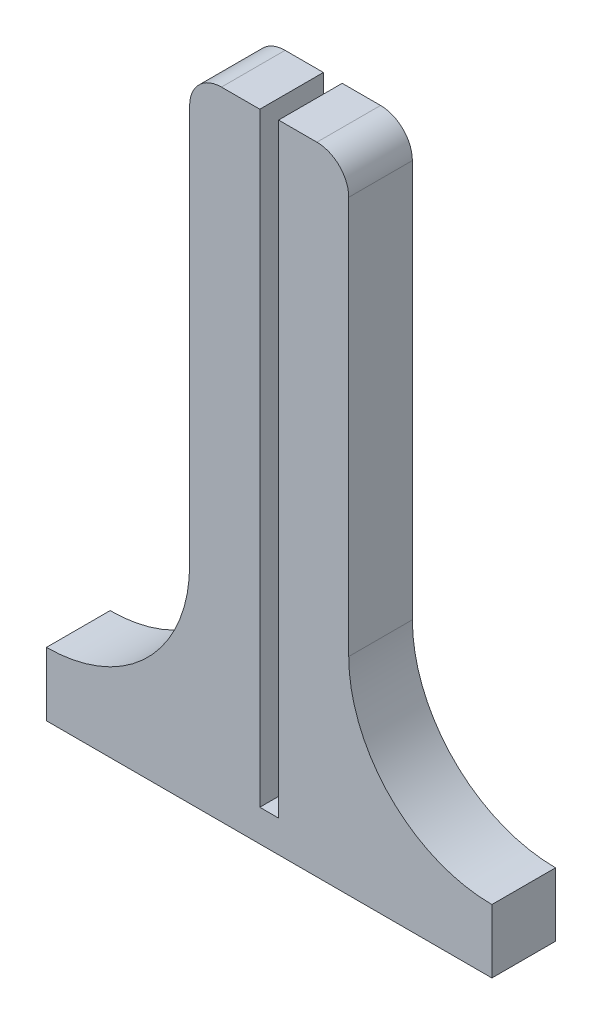
SolidWorks part; units mm, degrees
ref_plane "Plan de face" through (0, 0, 0) normal (0, 0, 1) x (1, 0, 0)
ref_plane "Plan de dessus" through (0, 0, 0) normal (0, 1, 0) x (1, 0, 0)
ref_plane "Plan de droite" through (0, 0, 0) normal (1, 0, 0) x (0, 0, -1)
sketch "Esquisse1" plane through (0, 0, 0) normal (0, 0, 1) x (1, 0, 0)
  line L0 (-70, 0) -> (70, 0)
  line L1 (70, 0) -> (70, 20)
  line L2 (25, 65) -> (25, 200)
  line L3 (25, 200) -> (-25, 200)
  line L4 (0, -36.4078) -> (0, 122.8519) construction
  line L5 (-70, 0) -> (-70, 20)
  line L6 (-25, 65) -> (-25, 200)
  arc A0 (70, 20) -> (25, 65) centre (70, 65) cw
  arc A1 (-70, 20) -> (-25, 65) centre (-70, 65) ccw
  point P4 (0, 0)
  point P15 (0, 200)
  dimension "D1" = 140
  dimension "D2" = 20
  dimension "D3" = 50
  dimension "D4" = 200
extrude "Boss.-Extru.1" add sketch "Esquisse1" along normal blind 20
fillet "Congé1" radius 10 2 edges at (-25, 200, 10) (25, 200, 10)
sketch "Esquisse2" plane through (0, 0, 20) normal (0, 0, 1) x (1, 0, 0)
  line L0 (-2.95, 10) -> (-2.95, 200)
  line L1 (-2.95, 10) -> (2.95, 10)
  line L2 (-2.95, 200) -> (2.95, 200)
  line L3 (2.95, 10) -> (2.95, 200)
  line L4 (-2.95, 10) -> (2.95, 200) construction
  line L5 (-2.95, 200) -> (2.95, 10) construction
  line L6 (-70, 0) -> (70, 0) construction
  line L7 (15, 200) -> (-15, 200) construction
  point P1 (0, 105)
  point P2 (0, 10)
  dimension "D1" = 5.9
  dimension "D2" = 10
extrude "Enlèv. mat.-Extru.1" cut sketch "Esquisse2" against normal blind 20
sketch "Esquisse3" plane through (-25, 0, 0) normal (-1, 0, 0) x (0, 0, 1)
  line L0 (10, 190) -> (10, 65) construction
  line L1 (20, 190) -> (0, 190) construction
  line L2 (20, 65) -> (0, 65) construction
  text T0 "Innovation Lab" font "Calibri" height 3.5
extrude "Enlèv. mat.-Extru.2" cut sketch "Esquisse3" against normal blind 0.6
